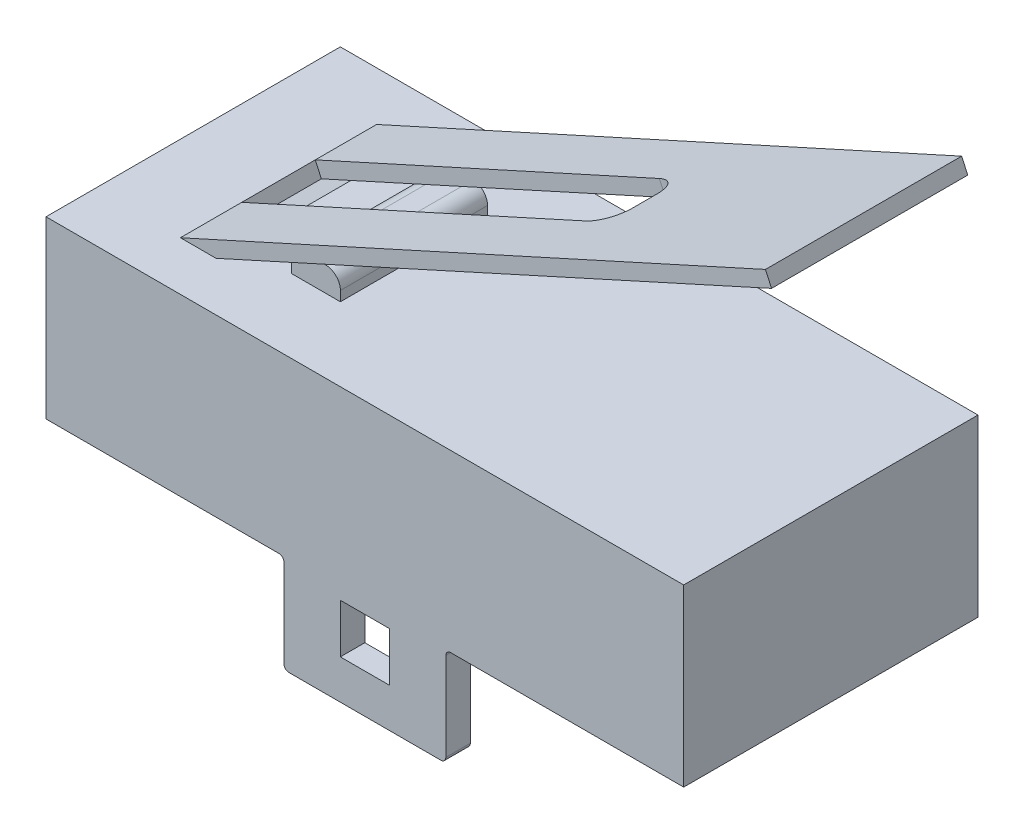
SolidWorks part; units mm, degrees
ref_plane "Piano frontale" through (0, 0, 0) normal (0, 0, 1) x (1, 0, 0)
ref_plane "Piano superiore" through (0, 0, 0) normal (0, 1, 0) x (1, 0, 0)
ref_plane "Piano destro" through (0, 0, 0) normal (1, 0, 0) x (0, 0, -1)
sketch "Schizzo1" plane through (0, 0, 0) normal (0, 0, 1) x (1, 0, 0)
  line L1 (-6.5, -1.785) -> (6.5, -1.785)
  line L2 (-6.5, -1.785) -> (-6.5, 1.785)
  line L3 (-6.5, 1.785) -> (6.5, 1.785)
  line L4 (6.5, -1.785) -> (6.5, 1.785)
  line L5 (-6.5, -1.785) -> (6.5, 1.785) construction
  line L6 (-6.5, 1.785) -> (6.5, -1.785) construction
  point P0 (0, 0)
  dimension "D1" = 13
  dimension "D2" = 3.57
extrude "Estrusione-Estrusione1" add sketch "Schizzo1" along normal blind 6
sketch "Schizzo3" plane through (0, -1.785, 0) normal (0, -1, 0) x (1, 0, 0)
  line L0 (-6.5, 6) -> (6.5, 6) construction
  line L1 (-1.65, 6) -> (1.65, 6)
  line L2 (-1.65, 6) -> (-1.65, 5.5)
  line L3 (-1.65, 5.5) -> (1.65, 5.5)
  line L4 (1.65, 6) -> (1.65, 5.5)
  line L5 (-6.5, 0) -> (6.5, 0) construction
  line L6 (-1.65, 0) -> (1.65, 0)
  line L7 (-1.65, 0) -> (-1.65, 0.5)
  line L8 (-1.65, 0.5) -> (1.65, 0.5)
  line L9 (1.65, 0) -> (1.65, 0.5)
  point P12 (0, 0.5)
  dimension "D1" = 0.5
  dimension "D2" = 0.5
  dimension "D3" = 3.3
extrude "Estrusione-Estrusione2" add sketch "Schizzo3" along normal blind 2
fillet "Raccordo1" radius 0.1 8 edges at (1.65, -3.785, 0.25) (-1.65, -3.785, 0.25) (-1.65, -3.785, 5.75) (1.65, -3.785, 5.75) (-1.65, -1.785, 0.25) (1.65, -1.785, 0.25)
sketch "Schizzo4" plane through (0, 0, 6) normal (0, 0, 1) x (1, 0, 0)
  line L0 (1.55, -3.785) -> (-1.55, -3.785) construction
  line L1 (-0.5, -1.985) -> (0.5, -1.985)
  line L2 (-0.5, -1.985) -> (-0.5, -2.985)
  line L3 (-0.5, -2.985) -> (0.5, -2.985)
  line L4 (0.5, -1.985) -> (0.5, -2.985)
  point P4 (0, -1.985)
  dimension "D1" = 1
  dimension "D2" = 1
  dimension "D3" = 0.8
extrude "Taglio-Estrusione1" cut sketch "Schizzo4" against normal through all
sketch "Schizzo5" plane through (0, 1.785, 0) normal (0, 1, 0) x (1, 0, 0)
  line L1 (-3, -1.5) -> (-1.9986, -1.5)
  line L2 (-3, -1.5) -> (-3, -4.5)
  line L3 (-3, -4.5) -> (-1.9986, -4.5)
  line L4 (-1.9986, -1.5) -> (-1.9986, -4.5)
  line L5 (6.5, 0) -> (-6.5, 0) construction
  line L6 (-6.5, -6) -> (-6.5, 0) construction
  dimension "D1" = 1.0014
  dimension "D2" = 3
  dimension "D3" = 1.5
  dimension "D4" = 3.5
extrude "Estrusione-Estrusione3" add sketch "Schizzo5" along normal blind 0.5
fillet "Raccordo2" radius 0.3 2 edges at (-3, 2.285, 3) (-1.9986, 2.285, 3)
ref_plane "Piano1" through (0, 0, 5) normal (0, 0, 1) x (1, 0, 0)
sketch "Schizzo7" plane through (0, 0, 5) normal (0, 0, 1) x (1, 0, 0)
  line L0 (-5.5, 1.285) -> (7.252, 7.063) construction
  line L1 (-6.5, 1.785) -> (-6.5, -1.785) construction
  line L2 (6.5, 1.785) -> (-6.5, 1.785) construction
  line L4 (-5.4283, 1.1528) -> (7.291, 6.916)
  line L5 (-5.5521, 1.4261) -> (7.1672, 7.1893)
  line L6 (-5.4283, 1.1528) -> (-5.5521, 1.4261)
  line L7 (7.291, 6.916) -> (7.1672, 7.1893)
  line L8 (-5.4902, 1.2894) -> (7.2291, 7.0526) construction
  dimension "D1" = 14
  dimension "D2" = 1
  dimension "D3" = 0.5
  dimension "D4" = 0.15
  dimension "D5" = 0.15
extrude "Estrusione-Estrusione4" add sketch "Schizzo7" against normal blind 4
sketch "Schizzo8" plane through (-1.4818, 3.2703, 0) normal (-0.4127, 0.9109, 0) x (0.9109, 0.4127, 0)
  line L0 (-3.5989, -5) -> (-3.5989, -1) construction
  line L1 (-3.5989, -2.25) -> (4.1011, -2.25)
  line L2 (-3.5989, -2.25) -> (-3.5989, -3.75)
  line L3 (-3.5989, -3.75) -> (4.1011, -3.75)
  line L4 (4.6011, -2.75) -> (4.6011, -3.25)
  line L5 (-3.0635, -5) -> (3.0635, -5) construction
  arc A0 (4.1011, -3.75) -> (4.6011, -3.25) centre (4.1011, -3.25) ccw
  arc A1 (4.1011, -2.25) -> (4.6011, -2.75) centre (4.1011, -2.75) cw
  point P10 (4.6011, -3.75)
  point P13 (4.6011, -2.25)
  dimension "D4" = 0.5
  dimension "D1" = 8.2
  dimension "D2" = 1.25
  dimension "D3" = 1.5
extrude "Taglio-Estrusione2" cut sketch "Schizzo8" against normal up to surface (0.3 mm away) up to face at (1.629, 4.3505, 3)
